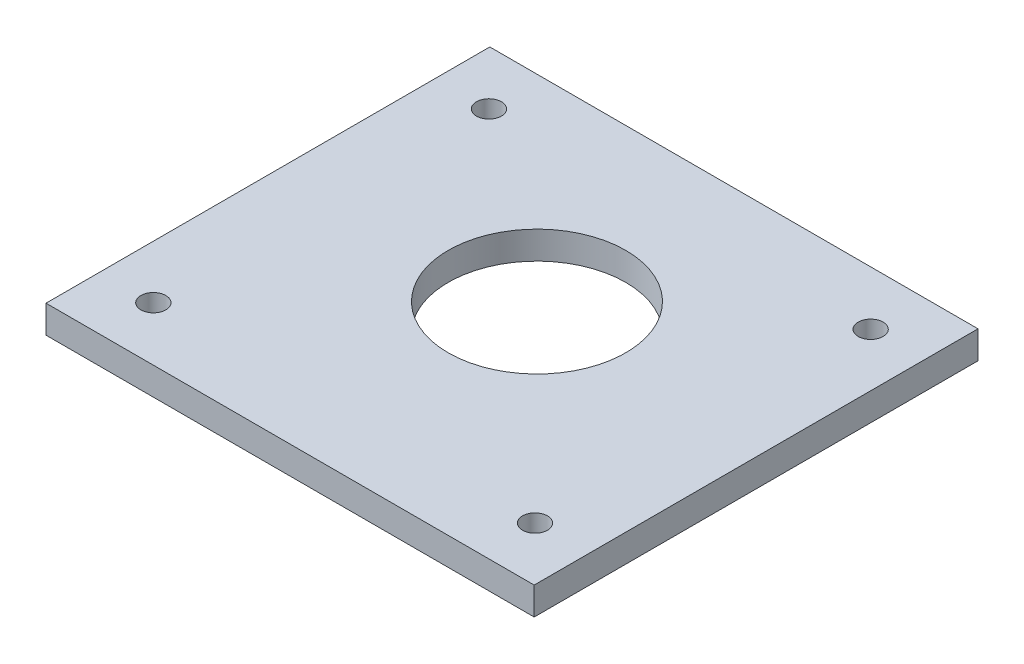
SolidWorks part; units mm, degrees
ref_plane "Спереди" through (0, 0, 0) normal (0, 0, 1) x (1, 0, 0)
ref_plane "Сверху" through (0, 0, 0) normal (0, 1, 0) x (1, 0, 0)
ref_plane "Справа" through (0, 0, 0) normal (1, 0, 0) x (0, 0, -1)
sketch "Эскиз1" plane through (0, 0, 0) normal (0, 1, 0) x (1, 0, 0)
  line L0 (-34.4, 45.4663) -> (-34.4, -37.5671) construction
  line L1 (-41.6086, 30.25) -> (64.5714, 30.25) construction
  line L2 (0, 66.5921) -> (0, -58.5092) construction
  line L3 (34.4, 45.4663) -> (34.4, -37.5671) construction
  line L4 (-93.5963, 0) -> (75.0424, 0) construction
  line L5 (-41.6086, -30.25) -> (64.5714, -30.25) construction
  line L7 (-44, 40) -> (44, 40)
  line L8 (-44, 40) -> (-44, -40)
  line L9 (-44, -40) -> (44, -40)
  line L10 (44, 40) -> (44, -40)
  line L11 (-44, 40) -> (44, -40) construction
  line L12 (-44, -40) -> (44, 40) construction
  circle A0 centre (-34.4, 30.25) radius 2.25
  circle A1 centre (34.4, 30.25) radius 2.25
  circle A2 centre (34.4, -30.25) radius 2.25
  circle A3 centre (-34.4, -30.25) radius 2.25
  circle A6 centre (0, 4.5) radius 16
  point P13 (0, 0)
  point P22 (0, 0)
  point P23 (0, 0)
  point P26 (0, 0)
  point P31 (0, 0)
  point P32 (0, 0)
  dimension "D1" = 80
  dimension "D3" = 32
  dimension "D4" = 68.8
  dimension "D5" = 35.5
  dimension "D6" = 60.5
  dimension "D7" = 4.5
  dimension "D2" = 88
extrude "Бобышка-Вытянуть1" add sketch "Эскиз1" along normal blind 5
sketch "Эскиз2" plane through (0, 5, 0) normal (0, 1, 0) x (1, 0, 0)
  line L0 (314.0837, 924.6268) -> (1752.0837, 924.6268) construction
